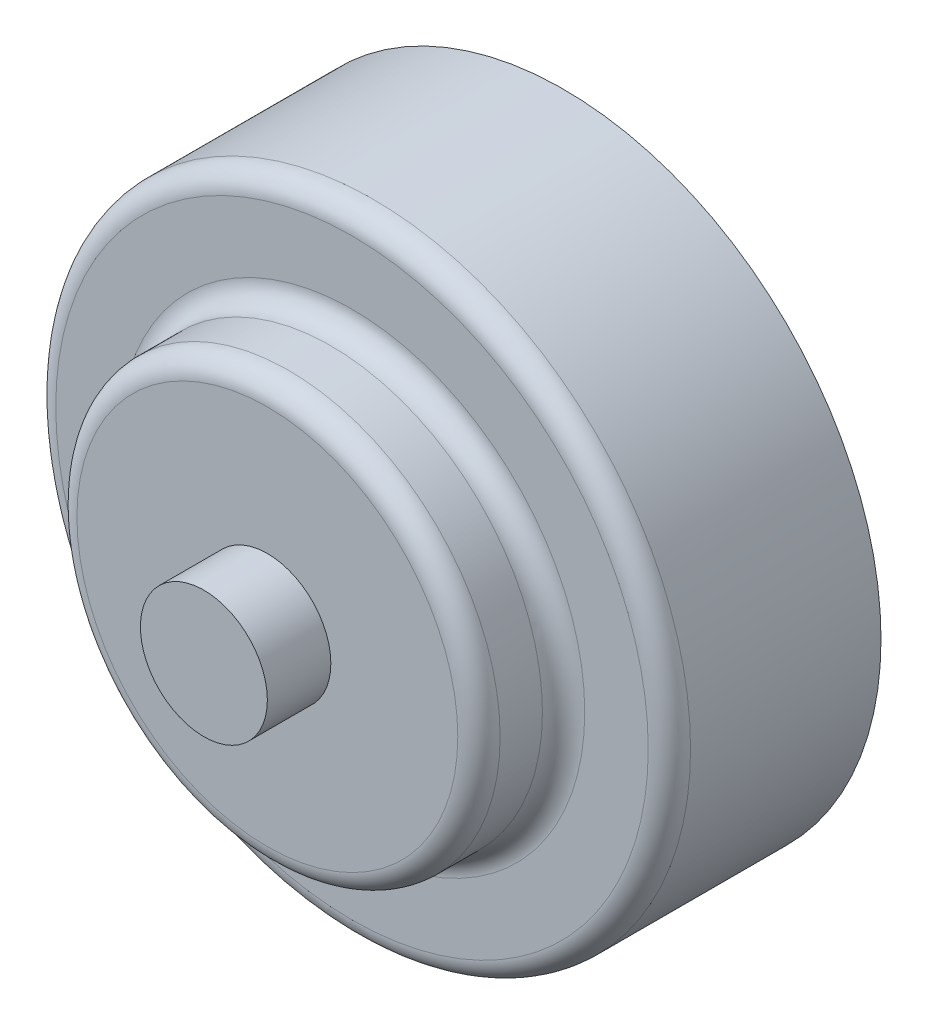
SolidWorks part; units mm, degrees
ref_plane "Front Plane" through (0, 0, 0) normal (0, 0, 1) x (1, 0, 0)
ref_plane "Top Plane" through (0, 0, 0) normal (0, 1, 0) x (1, 0, 0)
ref_plane "Right Plane" through (0, 0, 0) normal (1, 0, 0) x (0, 0, -1)
sketch "Sketch1" plane through (0, 0, 0) normal (0, 0, 1) x (1, 0, 0)
  circle A0 centre (0, 0) radius 75
  dimension "D1" = 150
extrude "Boss-Extrude1" add sketch "Sketch1" along normal blind 50
sketch "Sketch2" plane through (0, 0, 50) normal (0, 0, 1) x (1, 0, 0)
  circle A0 centre (0, 0) radius 50
  dimension "D1" = 100
extrude "Boss-Extrude2" add sketch "Sketch2" along normal blind 20
sketch "Sketch3" plane through (0, 0, 70) normal (0, 0, 1) x (1, 0, 0)
  circle A0 centre (0, 0) radius 15
  dimension "D1" = 30
extrude "Boss-Extrude3" add sketch "Sketch3" along normal blind 15
fillet "Fillet1" radius 5 3 edges at (50, 0, 70) (50, 0, 50) (75, 0, 50)
